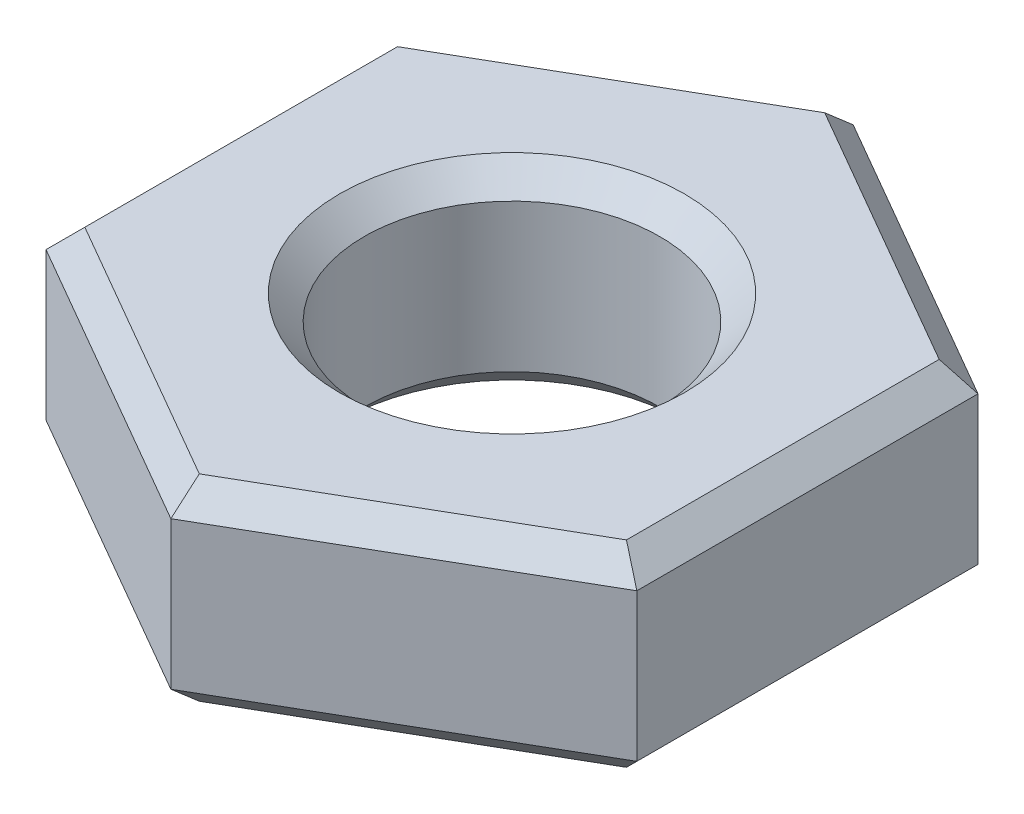
SolidWorks part; units mm, degrees
ref_plane "Front Plane" through (0, 0, 0) normal (0, 0, 1) x (1, 0, 0)
ref_plane "Top Plane" through (0, 0, 0) normal (0, 1, 0) x (1, 0, 0)
ref_plane "Right Plane" through (0, 0, 0) normal (1, 0, 0) x (0, 0, -1)
sketch "Sketch1" plane through (0, 0, 0) normal (0, 1, 0) x (1, 0, 0)
  line L1 (0, -3.4641) -> (3, -1.7321)
  line L2 (3, -1.7321) -> (3, 1.7321)
  line L3 (3, 1.7321) -> (0, 3.4641)
  line L4 (0, 3.4641) -> (-3, 1.7321)
  line L5 (-3, 1.7321) -> (-3, -1.7321)
  line L6 (-3, -1.7321) -> (0, -3.4641)
  circle A0 centre (0, 0) radius 3 construction
  circle A1 centre (0, 0) radius 1.5
  dimension "D2" = 3
  dimension "D1" = 6
extrude "Boss-Extrude1" add sketch "Sketch1" along normal blind 2
chamfer "Chamfer1" distance 0.25 angle 45 14 edges at (0, 0, 1.5) (1.5, 0, 2.5981) (3, 0, 0) (1.5, 0, -2.5981) (-1.5, 0, -2.5981) (-3, 0, 0) (-1.5, 0, 2.5981) (0, 2, 1.5) (-3, 2, 0) (-1.5, 2, -2.5981) (1.5, 2, -2.5981) (3, 2, 0) (1.5, 2, 2.5981) (-1.5, 2, 2.5981)
